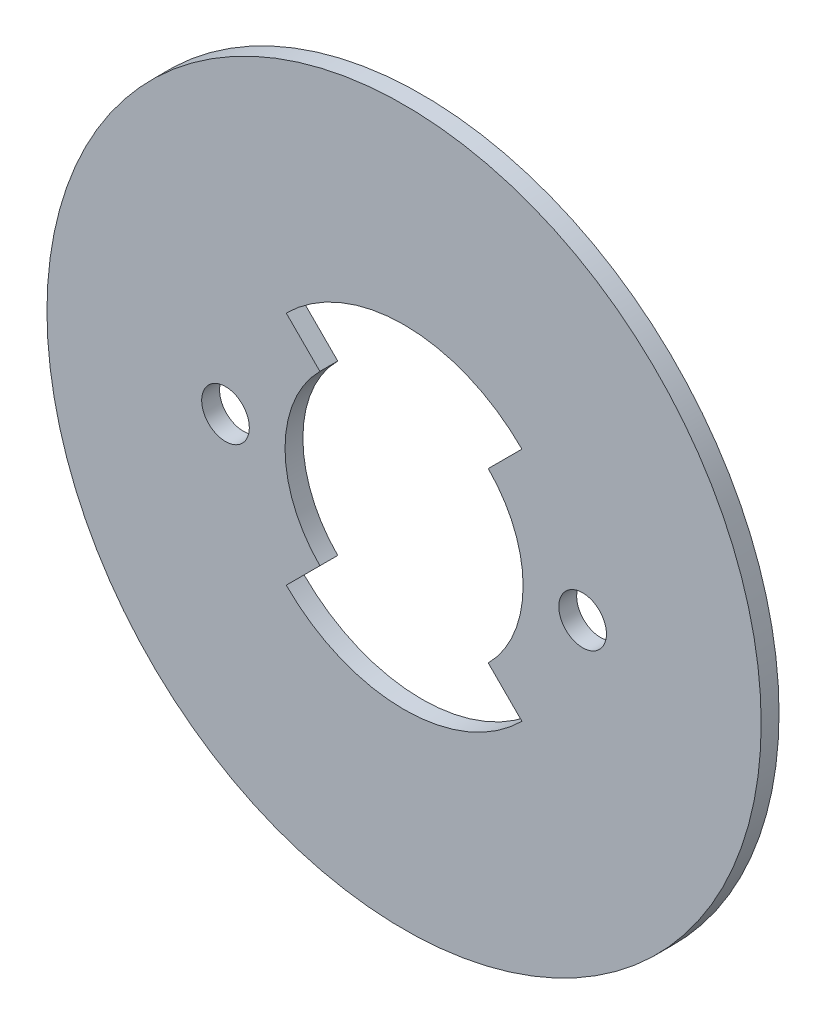
SolidWorks part; units mm, degrees
material "Chrome Stainless Steel"
ref_plane "Front Plane" through (0, 0, 0) normal (0, 0, 1) x (1, 0, 0)
ref_plane "Top Plane" through (0, 0, 0) normal (0, 1, 0) x (1, 0, 0)
ref_plane "Right Plane" through (0, 0, 0) normal (1, 0, 0) x (0, 0, -1)
sketch "Sketch1" plane through (0, 0, 0) normal (0, 0, 1) x (1, 0, 0)
  line L0 (0, 0) -> (30, 0) construction
  line L1 (0, 0) -> (-30, 0) construction
  circle A0 centre (0, 0) radius 30
  circle A1 centre (15, 0) radius 2
  circle A2 centre (-15, 0) radius 2
  dimension "D1" = 60
  dimension "D4" = 4
  dimension "D2" = 15
  dimension "D3" = 15
extrude "Boss-Extrude1" add sketch "Sketch1" along normal blind 1.5
sketch "Sketch2" plane through (0, 0, 0) normal (0, 0, -1) x (-1, 0, 0)
  line L0 (0, 0) -> (0, 14) construction
  line L1 (9.8995, 9.8995) -> (-9.8995, -9.8995)
  line L2 (-9.8995, 9.8995) -> (9.8995, -9.8995)
  circle A0 centre (0, 0) radius 14
  circle A1 centre (0, 0) radius 10
  point P9 (11.2786, -8.2941)
  dimension "D1" = 28
  dimension "D2" = 20
  dimension "D3" = 45
  dimension "D4" = 45
extrude "Cut-Extrude1" cut sketch "Sketch2" against normal blind 10 contours L2 L0 A1 | L2 A1 L1 | L1 A1 L2 | L2 A1 L1 | L0 L1 A1 | L0 A1 L1 A0 | A1 L0 A0 L2 | A1 L1 A0 L2
equation "\"D3@Sketch1\"=\"D2@Sketch1\""
equation "\"D4@Sketch2\"=\"D3@Sketch2\""
